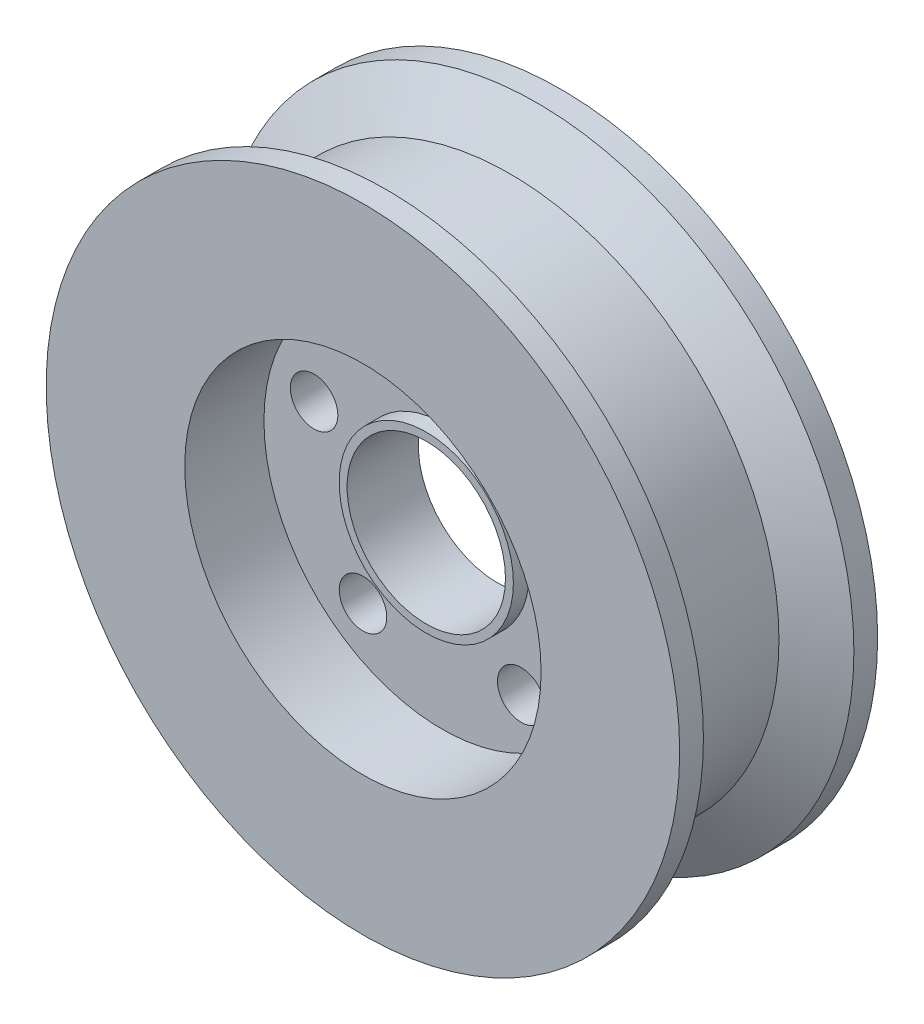
SolidWorks part; units mm, degrees
material "Stainless Steel (ferritic)"
ref_plane "Front Plane" through (0, 0, 0) normal (0, 0, 1) x (1, 0, 0)
ref_plane "Top Plane" through (0, 0, 0) normal (0, 1, 0) x (1, 0, 0)
ref_plane "Right Plane" through (0, 0, 0) normal (1, 0, 0) x (0, 0, -1)
sketch "Sketch1" plane through (0, 0, 0) normal (0, 0, 1) x (1, 0, 0)
  circle A0 centre (0, 0) radius 40
  circle A1 centre (0, 0) radius 10
  dimension "D1" = 80
  dimension "D2" = 20
extrude "Boss-Extrude1" add sketch "Sketch1" along normal mid plane 25
sketch "Sketch2" plane through (0, 0, 12.5) normal (0, 0, 1) x (1, 0, 0)
  circle A0 centre (0, 0) radius 22.5
  circle A1 centre (0, 0) radius 40 construction
  dimension "D1" = 17.5
extrude "Cut-Extrude1" cut sketch "Sketch2" against normal blind 10
mirror "Mirror1" about plane through (0, 0, 0) normal (0, 0, 1) of "Cut-Extrude1"
sketch "Sketch3" plane through (0, 0, 2.5) normal (0, 0, 1) x (1, 0, 0)
  circle A0 centre (0, 17) radius 3
  dimension "D1" = 6
  dimension "D2" = 17
extrude "Cut-Extrude2" cut sketch "Sketch3" against normal through all
pattern_circular "CirPattern1" count 5 over 360 about axis through (0, 0, 0) along (0, 0, 1) of "Cut-Extrude2"
sketch "Sketch4" plane through (0, 0, 0) normal (0, 1, 0) x (1, 0, 0)
  line L0 (0, 0) -> (0, 19.6279) construction
  line L1 (40, 9.5) -> (40, -9.5)
  line L2 (40, -12.5) -> (40, 12.5) construction
  line L3 (40, -9.5) -> (34, -6.0359)
  line L4 (34, -6.0359) -> (34, 6.0359)
  line L5 (34, 6.0359) -> (40, 9.5)
  line L6 (40, 12.5) -> (-40, 12.5) construction
  line L7 (-40, -12.5) -> (40, -12.5) construction
  dimension "D1" = 6
  dimension "D2" = 3
  dimension "D3" = 3
  dimension "D4" = 60
  dimension "D5" = 60
revolve "Cut-Revolve1" cut sketch "Sketch4" angle 360 about L0
sketch "Sketch5" plane through (0, 0, 2.5) normal (0, 0, 1) x (1, 0, 0)
  circle A0 centre (0, 0) radius 11
  circle A1 centre (0, 0) radius 10 construction
  circle A2 centre (0, 0) radius 10
  dimension "D1" = 22
extrude "Boss-Extrude2" add sketch "Sketch5" along normal blind 2 and the other way blind 7
